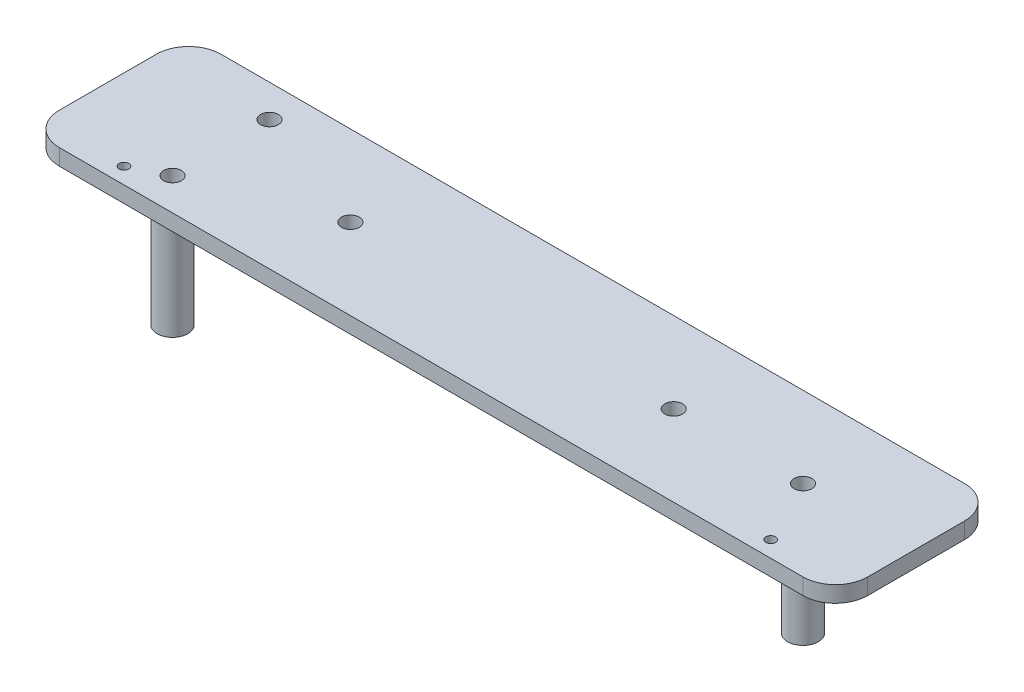
SolidWorks part; units mm, degrees
ref_plane "Front Plane" through (0, 0, 0) normal (0, 0, 1) x (1, 0, 0)
ref_plane "Top Plane" through (0, 0, 0) normal (0, 1, 0) x (1, 0, 0)
ref_plane "Right Plane" through (0, 0, 0) normal (1, 0, 0) x (0, 0, -1)
sketch "Sketch1" plane through (0, 0, 0) normal (0, 1, 0) x (1, 0, 0)
  line L0 (-90, 15) -> (90, 15) construction
  line L1 (-115, 25) -> (115, 25)
  line L2 (-125, 15) -> (-125, -15)
  line L3 (-115, -25) -> (115, -25)
  line L4 (125, 15) -> (125, -15)
  line L5 (-125, 25) -> (125, -25) construction
  line L6 (-125, -25) -> (125, 25) construction
  line L7 (90, 15) -> (90, 0) construction
  line L8 (0, 0) -> (0, -25) construction
  line L9 (-50, 0) -> (0, 0) construction
  circle A2 centre (90, 0) radius 2.75
  circle A3 centre (-90, 15) radius 2.75
  circle A4 centre (-50, 0) radius 2.75
  circle A6 centre (50, 0) radius 2.75
  circle A7 centre (-90, -15) radius 2.75
  arc A8 (115, 25) -> (125, 15) centre (115, 15) cw
  arc A9 (115, -25) -> (125, -15) centre (115, -15) ccw
  arc A10 (-125, -15) -> (-115, -25) centre (-115, -15) ccw
  arc A11 (-115, 25) -> (-125, 15) centre (-115, 15) ccw
  circle A12 centre (-100, -20) radius 1.5
  circle A13 centre (100, -20) radius 1.5
  point P0 (0, 0)
  point P12 (0, 15)
  dimension "D1" = 30
  dimension "D4" = 40
  dimension "D5" = 5.5
  dimension "D6" = 10
  dimension "D8" = 3
  dimension "D9" = 200
  dimension "D2" = 250
  dimension "D3" = 50
  dimension "D7" = 100
  dimension "D10" = 5
extrude "Boss-Extrude1" add sketch "Sketch1" along normal blind 5
sketch "Sketch2" plane through (0, 0, 0) normal (0, -1, 0) x (-1, 0, 0)
  line L0 (125, 0) -> (50, 0) construction
  line L1 (125, 15) -> (125, -15) construction
  circle A0 centre (90, -15) radius 4.75
  circle A1 centre (90, -15) radius 2.75
  circle A2 centre (90, 15) radius 4.75
  circle A3 centre (90, 15) radius 2.75
  circle A4 centre (90, -15) radius 2.75 construction
  circle A5 centre (-90, 0) radius 2.75
  circle A6 centre (-90, 0) radius 4.75
  circle A7 centre (-90, 0) radius 2.75 construction
  dimension "D1" = 2
extrude "Boss-Extrude2" add sketch "Sketch2" along normal blind 35
